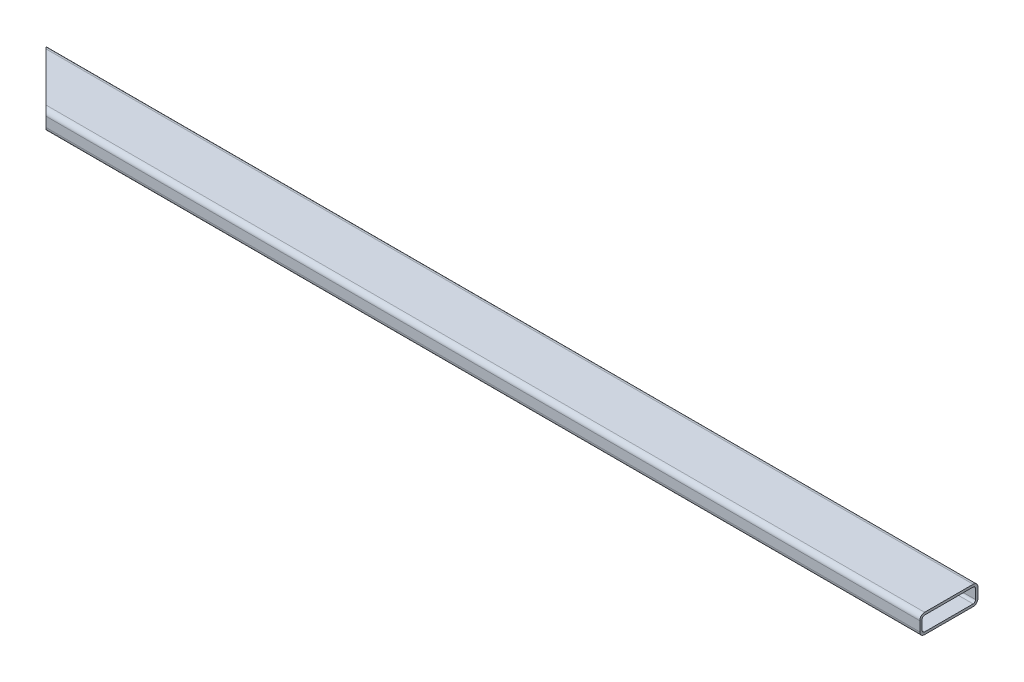
SolidWorks part; units mm, degrees
material "Alloy Steel"
ref_plane "Front Plane" through (0, 0, 0) normal (0, 0, 1) x (1, 0, 0)
ref_plane "Top Plane" through (0, 0, 0) normal (0, 1, 0) x (1, 0, 0)
ref_plane "Right Plane" through (0, 0, 0) normal (1, 0, 0) x (0, 0, -1)
sketch "Sketch1" plane through (0, 0, 0) normal (1, 0, 0) x (0, 0, -1)
  line L1 (0, 0) -> (76.2, 0)
  line L2 (0, 0) -> (0, 25.4)
  line L3 (0, 25.4) -> (76.2, 25.4)
  line L4 (76.2, 0) -> (76.2, 25.4)
  dimension "D1" = 25.4
  dimension "D2" = 76.2
extrude "Boss-Extrude1" add sketch "Sketch1" along normal blind 1219.2
fillet "Fillet1" radius 6.35 4 edges at (609.6, 0, -76.2) (609.6, 25.4, -76.2) (609.6, 0, 0) (609.6, 25.4, 0)
shell "Shell1" thickness 3.175
sketch "Sketch2" plane through (0, 25.4, 0) normal (0, 1, 0) x (1, 0, 0)
  line L0 (0, 76.2) -> (76.2, 0)
  line L1 (1219.2, 0) -> (0, 0) construction
  line L2 (0, 76.2) -> (0, 0)
  line L3 (0, 0) -> (76.2, 0)
  line L4 (0, 76.2) -> (1219.2, 76.2) construction
  dimension "D1" = 45
extrude "Cut-Extrude1" cut sketch "Sketch2" against normal blind 25.4
